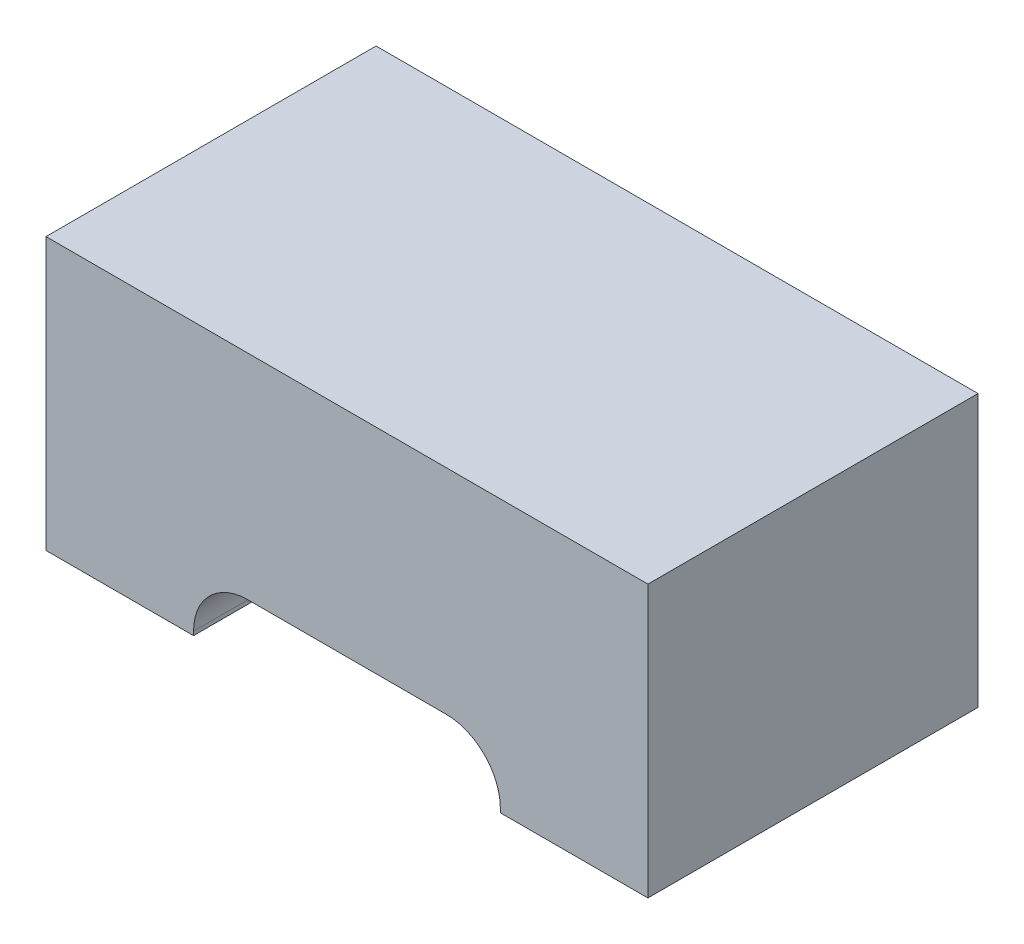
SolidWorks part; units mm, degrees
ref_plane "Front Plane" through (0, 0, 0) normal (0, 0, 1) x (1, 0, 0)
ref_plane "Top Plane" through (0, 0, 0) normal (0, 1, 0) x (1, 0, 0)
ref_plane "Right Plane" through (0, 0, 0) normal (1, 0, 0) x (0, 0, -1)
sketch "Sketch1" plane through (0, 0, 0) normal (0, 1, 0) x (1, 0, 0)
  line L1 (-0.775, -0.425) -> (0.775, -0.425)
  line L2 (-0.775, -0.425) -> (-0.775, 0.425)
  line L3 (-0.775, 0.425) -> (0.775, 0.425)
  line L4 (0.775, -0.425) -> (0.775, 0.425)
  line L5 (-0.775, -0.425) -> (0.775, 0.425) construction
  line L6 (-0.775, 0.425) -> (0.775, -0.425) construction
  point P0 (0, 0)
  dimension "D1" = 1.55
  dimension "D2" = 0.85
extrude "Boss-Extrude1" add sketch "Sketch1" along normal blind 0.7
sketch "Sketch2" plane through (0, 0, 0) normal (0, 0, 1) x (1, 0, 0)
  line L1 (-0.255, 0.15) -> (0.255, 0.15)
  line L2 (-0.395, 0.01) -> (-0.395, 0)
  line L3 (-0.395, 0) -> (0.395, 0)
  line L4 (0.395, 0.01) -> (0.395, 0)
  line L6 (-0.775, 0.7) -> (-0.775, 0) construction
  arc A0 (0.255, 0.15) -> (0.395, 0.01) centre (0.255, 0.01) cw
  arc A1 (-0.255, 0.15) -> (-0.395, 0.01) centre (-0.255, 0.01) ccw
  point P4 (0, 0)
  point P10 (0.395, 0.15)
  dimension "D3" = 0.14
  dimension "D1" = 0.38
  dimension "D2" = 0.15
extrude "Cut-Extrude1" cut sketch "Sketch2" against normal through all both and the other way through all
